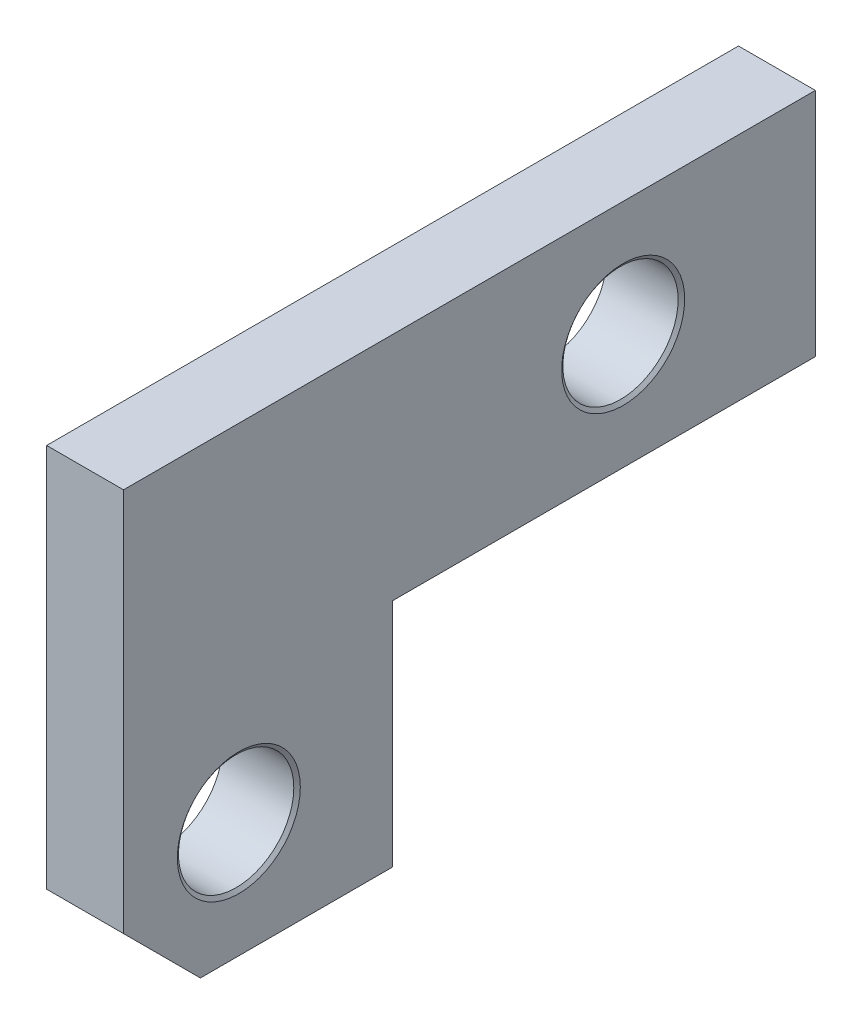
SolidWorks part; units mm, degrees
material "Простая углеродистая сталь"
ref_plane "Спереди" through (0, 0, 0) normal (0, 0, 1) x (1, 0, 0)
ref_plane "Сверху" through (0, 0, 0) normal (0, 1, 0) x (1, 0, 0)
ref_plane "Справа" through (0, 0, 0) normal (1, 0, 0) x (0, 0, -1)
sketch "Эскиз1" plane through (0, 0, 0) normal (1, 0, 0) x (0, 0, -1)
  line L0 (-2, -6) -> (-2, 0)
  line L1 (-9, -6) -> (9, -6)
  line L2 (-9, -6) -> (-9, 6)
  line L3 (-9, 6) -> (9, 6)
  line L4 (9, -6) -> (9, 6)
  line L5 (-9, -6) -> (9, 6) construction
  line L6 (-9, 6) -> (9, -6) construction
  line L7 (-2, 0) -> (9, 0)
  point P0 (0, 0)
  dimension "D1" = 18
  dimension "D2" = 12
  dimension "D3" = 6
  dimension "D4" = 7
extrude "Бобышка-Вытянуть1" add sketch "Эскиз1" along normal blind 2 contours L0 L7 L4 L3 L2 L1
hole_wizard "Отверстие обработанное метчиком M31" positions "Эскиз3" profile "Эскиз2" tap size "M3" standard "DIN" end condition through all
sketch "Эскиз3" plane through (2, 0.9913, -4.4979) normal (1, 0, 0) x (0, 0, -1)
  line L3 (-13.4979, -6.9913) -> (-13.4979, 5.0087) construction
  line L4 (-13.4979, -6.9913) -> (-6.4979, -6.9913) construction
  point P0 (-0.4979, 2.0087)
  point P1 (-10.4979, -3.9913)
  dimension "D1" = 3
  dimension "D2" = 3
  dimension "D3" = 6
  dimension "D4" = 10
sketch "Эскиз2" plane through (2, 3, -4) normal (0, 1, 0) x (0, 0, -1)
  line L0 (0, 0) -> (0, 2)
  line L1 (0, 2) -> (1.6, 2)
  line L2 (1.5, 1.93) -> (1.5, 0.07)
  line L3 (1.5, 0.07) -> (1.6, 0)
  line L5 (1.6, 0) -> (0, 0)
  line L6 (-1.5, 0.07) -> (-1.6, 0) construction
  line L7 (1.6, 2) -> (1.5, 1.93)
  line L8 (-1.6, 2) -> (-1.5, 1.93) construction
  line L11 (0, -6.35) -> (0, 107.95) construction
  dimension "Диаметр резьбы" = 3
  dimension "Глубина проходного сверла" = 2
  dimension "Диаметр передней зенковки" = 3.2
  dimension "Угол передней зенковки" = 110
  dimension "Диаметр задней зенковки" = 3.2
  dimension "Угол задней зенковки" = 110
chamfer "Фаска2" distance 2 angle 45 1 edges at (1, -6, 9)
